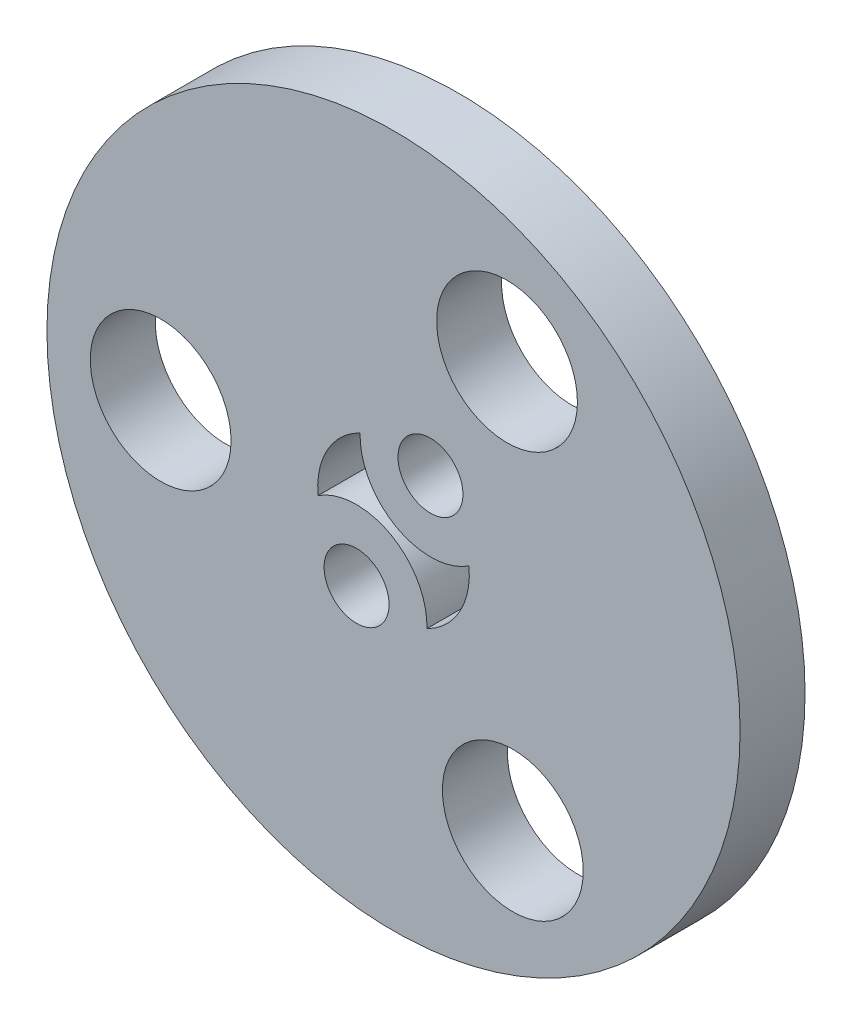
SolidWorks part; units mm, degrees
ref_plane "Plan de face" through (0, 0, 0) normal (0, 0, 1) x (1, 0, 0)
ref_plane "Plan de dessus" through (0, 0, 0) normal (0, 1, 0) x (1, 0, 0)
ref_plane "Plan de droite" through (0, 0, 0) normal (1, 0, 0) x (0, 0, -1)
sketch "Esquisse1" plane through (0, 0, 0) normal (0, 0, 1) x (1, 0, 0)
  line L0 (5.2405, 9.3862) -> (0, 0) construction
  line L1 (-10.7489, -0.1547) -> (5.2405, 9.3862) construction
  line L2 (5.2405, 9.3862) -> (5.5084, -9.2314) construction
  line L3 (5.5084, -9.2314) -> (-10.7489, -0.1547) construction
  line L4 (0, 0) -> (-2.6202, -4.6931) construction
  circle A0 centre (0, 0) radius 16
  circle A13 centre (5.5084, -9.2314) radius 3.25
  circle A26 centre (0, 0) radius 7.5 construction
  circle A28 centre (-10.7489, -0.1547) radius 3.25
  circle A29 centre (5.2405, 9.3862) radius 3.25
  circle A30 centre (1.7062, 3.056) radius 1.5
  circle A31 centre (-1.7062, -3.056) radius 1.5
  arc A32 (-1.5427, 3.1417) -> (3.4839, 0.3353) centre (1.7062, 3.056) ccw
  arc A33 (1.5427, -3.1417) -> (-3.4839, -0.3353) centre (-1.7062, -3.056) ccw
  arc A34 (-1.5427, 3.1417) -> (-3.4839, -0.3353) centre (0, 0) ccw
  arc A35 (1.5427, -3.1417) -> (3.4839, 0.3353) centre (0, 0) ccw
  point P9 (-1.7062, -3.056)
  point P13 (1.7062, 3.056)
  point P32 (0, 0)
  dimension "D1" = 32
  dimension "D2" = 15
  dimension "D5" = 6.5
  dimension "D7" = 6.5
  dimension "D9" = 3.5
  dimension "D10" = 3.5
  dimension "D11" = 6.5
  dimension "D12" = 6.5
  dimension "D14" = 3
  dimension "D8" = 6.5
  dimension "D13" = 3
  dimension "D6" = 10.75
extrude "Boss.-Extru.1" add sketch "Esquisse1" along normal blind 3
